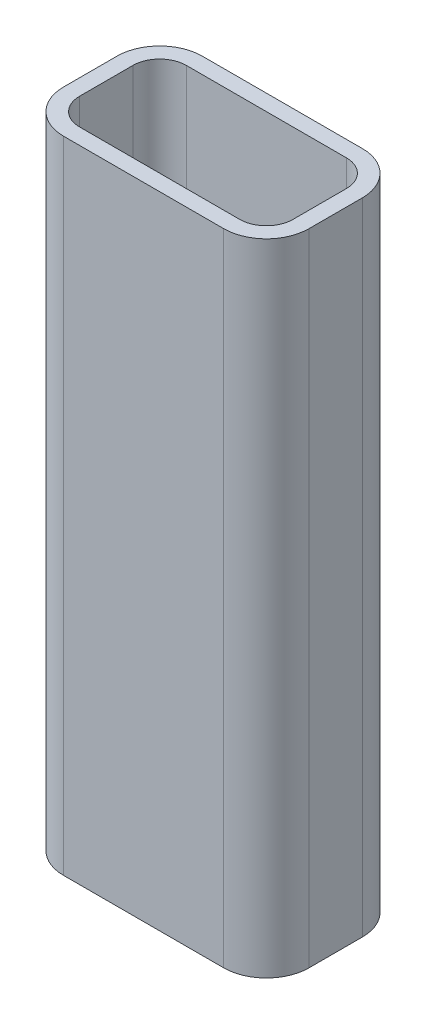
SolidWorks part; units mm, degrees
ref_plane "Front Plane" through (0, 0, 0) normal (0, 0, 1) x (1, 0, 0)
ref_plane "Top Plane" through (0, 0, 0) normal (0, 1, 0) x (1, 0, 0)
ref_plane "Right Plane" through (0, 0, 0) normal (1, 0, 0) x (0, 0, -1)
sketch "Sketch1" plane through (0, 0, 0) normal (0, 1, 0) x (1, 0, 0)
  line L1 (-15, 10) -> (15, 10)
  line L2 (-20, 5) -> (-20, -5)
  line L3 (-15, -10) -> (15, -10)
  line L4 (20, 5) -> (20, -5)
  line L5 (-20, 10) -> (20, -10) construction
  line L6 (-20, -10) -> (20, 10) construction
  arc A0 (-15, 10) -> (-20, 5) centre (-15, 5) ccw
  arc A1 (15, 10) -> (20, 5) centre (15, 5) cw
  arc A2 (-20, -5) -> (-15, -10) centre (-15, -5) ccw
  arc A3 (15, -10) -> (20, -5) centre (15, -5) ccw
  point P0 (0, 0)
  dimension "D3" = 5
  dimension "D4" = 5
  dimension "D5" = 5
  dimension "D6" = 5
  dimension "D1" = 40
  dimension "D2" = 20
extrude "Extrude-Thin1" add sketch "Sketch1" along normal mid plane 120 thin thin type one direction wall 3
sketch "Sketch2" plane through (0, 0, 0) normal (0, 0, 1) x (1, 0, 0)
  line L0 (0, 47.2662) -> (0, -42.7338) construction
  line L1 (6, 47.2662) -> (6, -42.7338)
  line L2 (-6, 47.2662) -> (-6, -42.7338)
  arc A0 (6, 47.2662) -> (-6, 47.2662) centre (0, 47.2662) ccw
  arc A1 (-6, -42.7338) -> (6, -42.7338) centre (0, -42.7338) ccw
  point P3 (0, 2.2662)
  dimension "D2" = 6
  dimension "D1" = 90
extrude "Cut-Extrude1" [suppressed] cut sketch "Sketch2" against normal through all and the other way through all contours L2 A1 L1 A0
